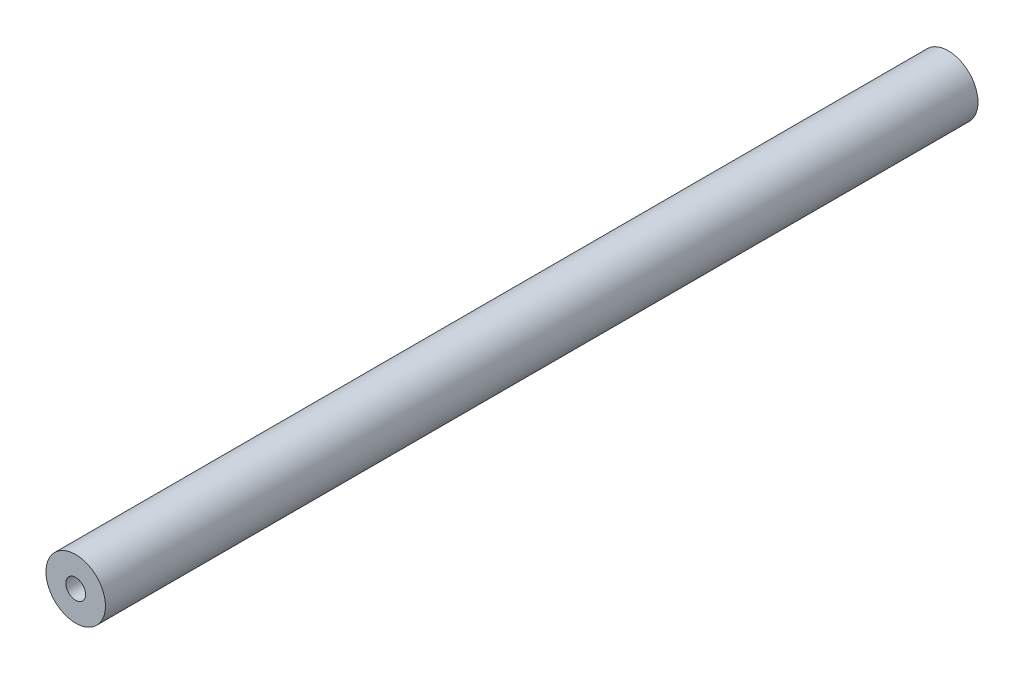
SolidWorks part; units mm, degrees
ref_plane "Front Plane" through (0, 0, 0) normal (0, 0, 1) x (1, 0, 0)
ref_plane "Top Plane" through (0, 0, 0) normal (0, 1, 0) x (1, 0, 0)
ref_plane "Right Plane" through (0, 0, 0) normal (1, 0, 0) x (0, 0, -1)
sketch "Sketch1" plane through (0, 0, 0) normal (0, 0, 1) x (1, 0, 0)
  circle A0 centre (0, 0) radius 4.7625
  circle A1 centre (0, 0) radius 1.5875
  dimension "D1" = 9.525
  dimension "D2" = 3.175
extrude "Boss-Extrude1" add sketch "Sketch1" along normal blind 139.7
